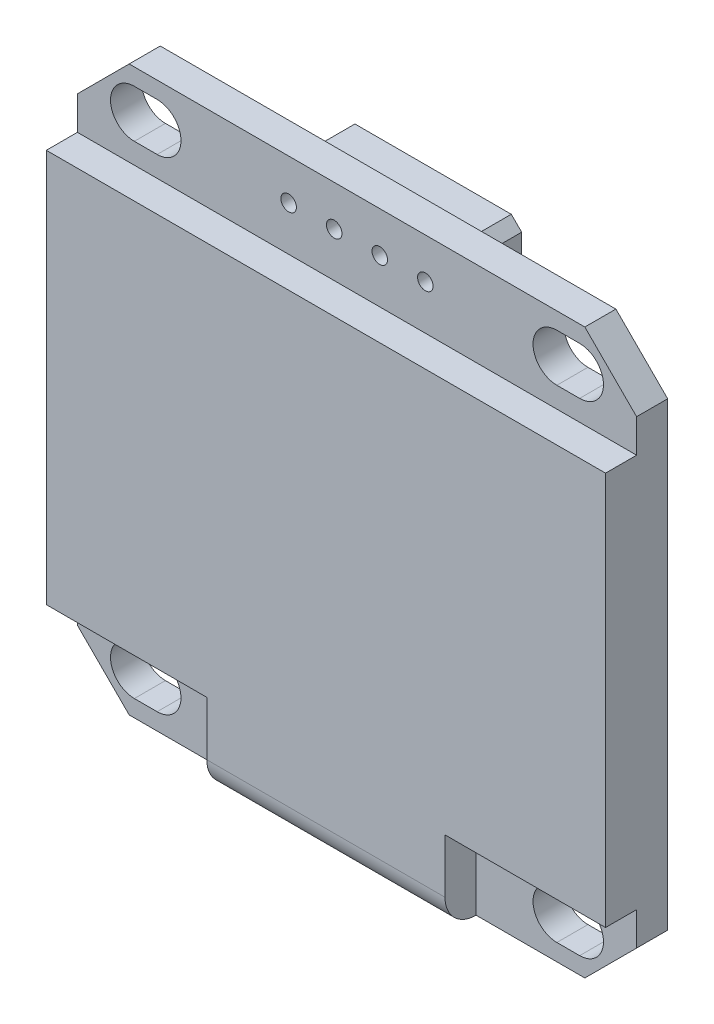
SolidWorks part; units mm, degrees
ref_plane "Face" through (0, 0, 0) normal (0, 0, 1) x (1, 0, 0)
ref_plane "Dessus" through (0, 0, 0) normal (0, 1, 0) x (1, 0, 0)
ref_plane "Droite" through (0, 0, 0) normal (1, 0, 0) x (0, 0, -1)
sketch "Esquisse1" plane through (0, 0, 0) normal (0, 0, 1) x (1, 0, 0)
  line L0 (2.75, 21.3) -> (3.85, 21.3) construction
  line L1 (0, 0) -> (27, 0) construction
  line L2 (0, 0) -> (0, 19.3) construction
  line L3 (0, 19.3) -> (27, 19.3) construction
  line L4 (27, 0) -> (27, 19.3) construction
  line L5 (2.75, 22.45) -> (3.85, 22.45)
  line L6 (2.75, 20.15) -> (3.85, 20.15)
  line L7 (13.5, 19.3) -> (13.5, 0) construction
  line L8 (0, 9.65) -> (27, 9.65) construction
  line L9 (24.25, 21.3) -> (23.15, 21.3) construction
  line L10 (24.25, 22.45) -> (23.15, 22.45)
  line L11 (24.25, 20.15) -> (23.15, 20.15)
  line L12 (24.25, -2) -> (23.15, -2) construction
  line L13 (24.25, -3.15) -> (23.15, -3.15)
  line L14 (24.25, -0.85) -> (23.15, -0.85)
  line L15 (2.75, -2) -> (3.85, -2) construction
  line L16 (2.75, -3.15) -> (3.85, -3.15)
  line L17 (2.75, -0.85) -> (3.85, -0.85)
  line L18 (8.55, 21.3) -> (18.45, 21.3) construction
  line L19 (8.55, 22.55) -> (18.45, 22.55) construction
  line L20 (8.55, 22.55) -> (8.55, 20.05) construction
  line L21 (8.55, 20.05) -> (18.45, 20.05) construction
  line L22 (18.45, 22.55) -> (18.45, 20.05) construction
  line L23 (13.5, 22.55) -> (13.5, 20.05) construction
  line L24 (0, -1.46) -> (2.5, -3.96)
  line L25 (9.1, 22.4) -> (11.3, 22.4) construction
  line L26 (9.1, 22.4) -> (9.1, 20.2) construction
  line L27 (9.1, 20.2) -> (11.3, 20.2) construction
  line L28 (11.3, 22.4) -> (11.3, 20.2) construction
  line L29 (9.1, 22.4) -> (11.3, 20.2) construction
  line L30 (9.1, 20.2) -> (11.3, 22.4) construction
  line L31 (2.5, 23.26) -> (24.5, 23.26)
  line L32 (0, 20.76) -> (0, -1.46)
  line L33 (2.5, -3.96) -> (24.5, -3.96)
  line L34 (27, 20.76) -> (27, -1.46)
  line L35 (0, 23.26) -> (27, -3.96) construction
  line L36 (0, -3.96) -> (27, 23.26) construction
  line L37 (24.5, -3.96) -> (27, -1.46)
  line L38 (24.5, 23.26) -> (27, 20.76)
  line L39 (0, 20.76) -> (2.5, 23.26)
  arc A0 (2.75, 22.45) -> (2.75, 20.15) centre (2.75, 21.3) ccw
  arc A1 (3.85, 20.15) -> (3.85, 22.45) centre (3.85, 21.3) ccw
  arc A2 (24.25, 22.45) -> (24.25, 20.15) centre (24.25, 21.3) cw
  arc A3 (23.15, 20.15) -> (23.15, 22.45) centre (23.15, 21.3) cw
  arc A4 (24.25, -3.15) -> (24.25, -0.85) centre (24.25, -2) ccw
  arc A5 (23.15, -0.85) -> (23.15, -3.15) centre (23.15, -2) ccw
  arc A6 (2.75, -3.15) -> (2.75, -0.85) centre (2.75, -2) cw
  arc A7 (3.85, -0.85) -> (3.85, -3.15) centre (3.85, -2) cw
  circle A8 centre (10.2, 21.3) radius 0.375
  circle A9 centre (12.4, 21.3) radius 0.375
  circle A10 centre (14.6, 21.3) radius 0.375
  circle A11 centre (16.8, 21.3) radius 0.375
  point P7 (3.3, 21.3)
  point P15 (13.5, 19.3)
  point P20 (23.7, 21.3)
  point P26 (10.2, 21.3)
  point P27 (12.4, 21.3)
  point P31 (23.7, -2)
  point P38 (3.3, -2)
  point P47 (14.4558, 20.9865)
  point P48 (14.6, 21.3)
  point P49 (16.8, 21.3)
  point P64 (10.2, 21.3)
  point P73 (13.5, 9.65)
  dimension "D1" = 3.4
  dimension "D6" = 17
  dimension "D8" = 0.75
  dimension "D2" = 2.3
  dimension "D3" = 19.3
  dimension "D4" = 27
  dimension "D5" = 21
  dimension "D10" = 9.9
  dimension "D11" = 2.5
  dimension "D12" = 2.2
  dimension "D13" = 27
  dimension "D14" = 27.22
  dimension "D7" = 4
  dimension "D9" = 4
extrude "Boss.-Extru.1" add sketch "Esquisse1" along normal blind 1.5
sketch "Esquisse2" plane through (0, 0, 1.5) normal (0, 0, 1) x (1, 0, 0)
  line L0 (27, -1.46) -> (27, 20.76) construction
  line L1 (0, 19.15) -> (27, 19.15)
  line L2 (0, 19.15) -> (0, 0.15)
  line L3 (0, 0.15) -> (7.75, 0.15)
  line L4 (27, 19.15) -> (27, 0.15)
  line L5 (0, 19.15) -> (27, 0.15) construction
  line L6 (0, 0.15) -> (27, 19.15) construction
  line L7 (0, 20.76) -> (0, -1.46) construction
  line L10 (27, 9.65) -> (0, 9.65) construction
  line L11 (2.5, -3.96) -> (24.5, -3.96) construction
  line L13 (7.75, 0.15) -> (7.75, -3.96)
  line L14 (7.75, -3.96) -> (19.25, -3.96)
  line L15 (19.25, 0.15) -> (19.25, -3.96)
  line L16 (7.75, 0.15) -> (19.25, -3.96) construction
  line L17 (7.75, -3.96) -> (19.25, 0.15) construction
  line L18 (19.25, 0.15) -> (27, 0.15)
  point P4 (13.5, 9.65)
  point P19 (13.5, -1.905)
  dimension "D1" = 19
  dimension "D2" = 11.5
extrude "Boss.-Extru.2" add sketch "Esquisse2" along normal blind 1.5
fillet "Congé1" radius 1.5 1 edges at (13.5, -3.96, 3)
sketch "Esquisse3" plane through (0, 0, 0) normal (0, 0, -1) x (-1, 0, 0)
  line L0 (-9.1, 22.4) -> (-11.3, 22.4) construction
  line L1 (-9.1, 22.4) -> (-9.1, 20.2) construction
  line L2 (-9.1, 20.2) -> (-11.3, 20.2) construction
  line L3 (-17.65, 20.7) -> (-17.15, 20.2)
  line L4 (-9.6, 22.4) -> (-11.3, 22.4)
  line L5 (-9.1, 21.9) -> (-9.1, 20.7)
  line L6 (-9.6, 20.2) -> (-11.3, 20.2)
  line L8 (-11.3, 22.4) -> (-13.5, 22.4)
  line L10 (-11.3, 20.2) -> (-13.5, 20.2)
  line L12 (-13.5, 22.4) -> (-15.45, 22.4)
  line L14 (-13.5, 20.2) -> (-15.45, 20.2)
  line L16 (-15.45, 22.4) -> (-17.15, 22.4)
  line L17 (-17.65, 21.9) -> (-17.65, 20.7)
  line L18 (-15.45, 20.2) -> (-17.15, 20.2)
  line L20 (-11.05, 21.9) -> (-11.05, 20.7) [skipped]
  line L21 (-13, 21.9) -> (-13, 20.7) [skipped]
  line L22 (-14.95, 21.9) -> (-14.95, 20.7) [skipped]
  line L23 (-17.15, 22.4) -> (-17.65, 21.9)
  line L24 (-9.1, 21.9) -> (-9.6, 22.4)
  line L25 (-9.1, 20.7) -> (-9.6, 20.2)
  line L26 (-13.5, 22.55) -> (-13.5, 20.05) construction
  circle A0 centre (-10.2, 21.3) radius 0.375 construction
  circle A1 centre (-16.8, 21.3) radius 0.375 construction
  circle A2 centre (-12.4, 21.3) radius 0.375 construction
  circle A3 centre (-10.2, 21.3) radius 0.375
  circle A4 centre (-16.8, 21.3) radius 0.375
  circle A5 centre (-12.4, 21.3) radius 0.375
  circle A6 centre (-14.6, 21.3) radius 0.375 construction
  circle A7 centre (-14.6, 21.3) radius 0.375
  point P26 (-17.65, 22.4)
  point P28 (-17.65, 20.2)
  dimension "D1" = 4
extrude "Boss.-Extru.3" add sketch "Esquisse3" along normal blind 2.3
